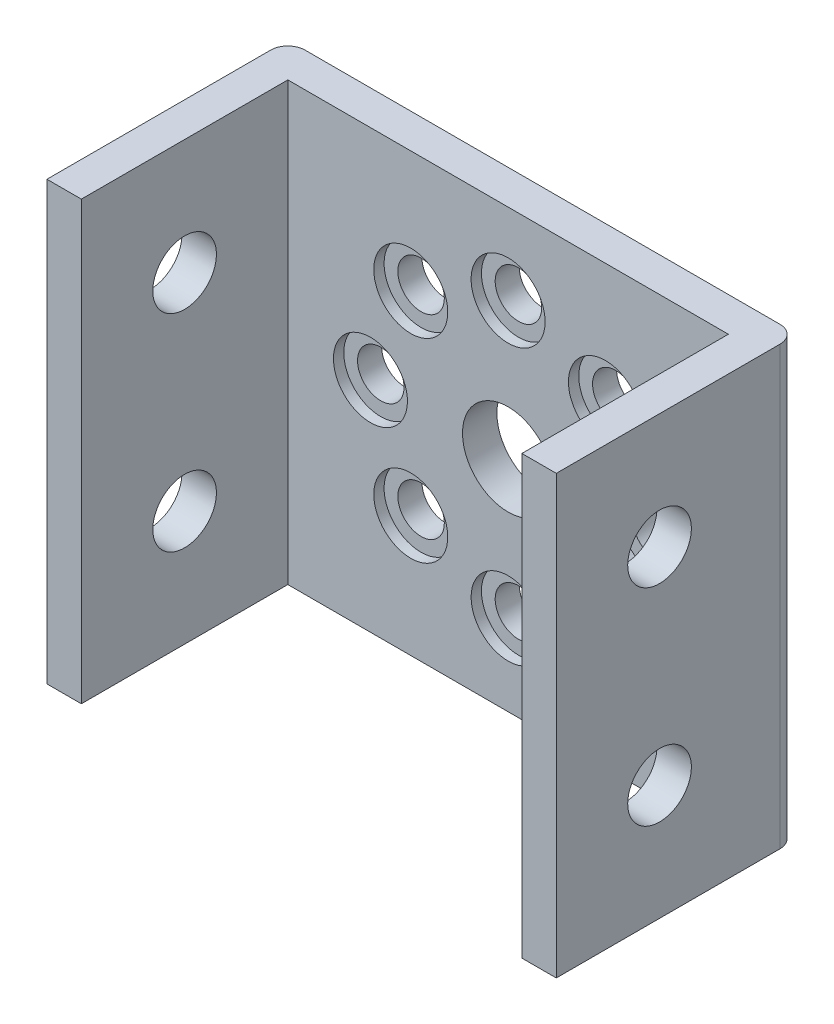
SolidWorks part; units mm, degrees
ref_plane "Front Plane" through (0, 0, 0) normal (0, 0, 1) x (1, 0, 0)
ref_plane "Top Plane" through (0, 0, 0) normal (0, 1, 0) x (1, 0, 0)
ref_plane "Right Plane" through (0, 0, 0) normal (1, 0, 0) x (0, 0, -1)
sketch "Sketch1" plane through (0, 0, 0) normal (0, 1, 0) x (1, 0, 0)
  line L0 (0, 0) -> (0, 31.75) construction
  line L1 (-14.8, 0) -> (14.8, 0)
  line L2 (14.8, 0) -> (14.8, -14)
  line L3 (14.8, -14) -> (12.8, -14)
  line L4 (12.8, -14) -> (12.8, -2)
  line L5 (12.8, -2) -> (-12.8, -2)
  line L6 (-12.8, -2) -> (-12.8, -14)
  line L7 (-12.8, -14) -> (-14.8, -14)
  line L8 (-14.8, -14) -> (-14.8, 0)
  dimension "D1" = 2
  dimension "D2" = 29.6
  dimension "D3" = 2
  dimension "D4" = 12
extrude "Boss-Extrude1" add sketch "Sketch1" along normal mid plane 25.4
sketch "Sketch2" plane through (-14.8, 0, 0) normal (-1, 0, 0) x (0, 0, 1)
  line L0 (0, 0) -> (21.026, 0) construction
  line L1 (0, 12.7) -> (0, -12.7) construction
  circle A0 centre (8, -6) radius 1.85
  circle A1 centre (8, 6) radius 1.85
  dimension "D1" = 3.7
  dimension "D2" = 12
  dimension "D3" = 8
extrude "Cut-Extrude1" cut sketch "Sketch2" against normal through all
sketch "Sketch3" plane through (0, 0, 0) normal (0, 0, -1) x (-1, 0, 0)
  circle A0 centre (0, 0) radius 2.65
  dimension "D1" = 5.3
extrude "Cut-Extrude2" cut sketch "Sketch3" against normal through all
sketch "Sketch4" plane through (0, 0, 2) normal (0, 0, 1) x (1, 0, 0)
  line L0 (0, 0) -> (0, 13.4152) construction
  line L1 (0, 0) -> (18.1171, 0) construction
  circle A0 centre (0, 8) radius 1.35
  dimension "D1" = 2.7
  dimension "D2" = 8
extrude "Cut-Extrude3" cut sketch "Sketch4" against normal through all
sketch "Sketch5" plane through (0, 0, 2) normal (0, 0, 1) x (1, 0, 0)
  circle A0 centre (0, 8) radius 2.15
  dimension "D1" = 4.3
extrude "Cut-Extrude4" cut sketch "Sketch5" against normal blind 0.6
pattern_circular "CirPattern1" count 8 over 360 about axis through (0, 0, 0) along (0, 0, 1) of "Cut-Extrude3", "Cut-Extrude4"
fillet "Fillet1" radius 1 2 edges at (14.8, 0, 0) (-14.8, 0, 0)
